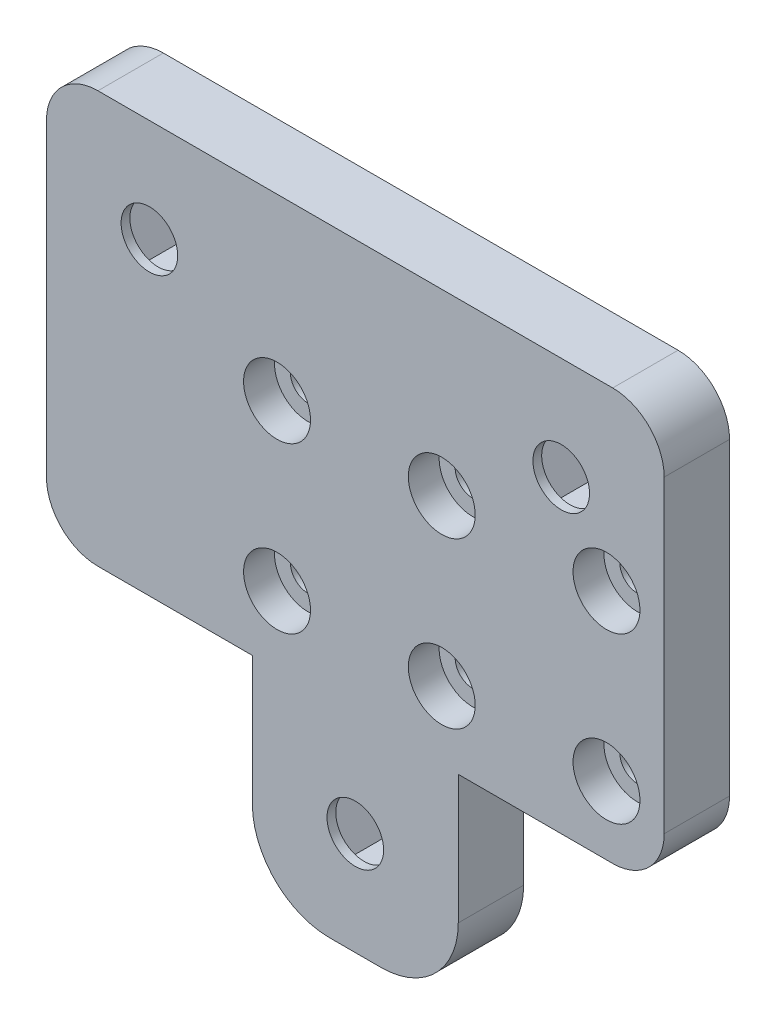
SolidWorks part; units mm, degrees
ref_plane "Front Plane" through (0, 0, 0) normal (0, 0, 1) x (1, 0, 0)
ref_plane "Top Plane" through (0, 0, 0) normal (0, 1, 0) x (1, 0, 0)
ref_plane "Right Plane" through (0, 0, 0) normal (1, 0, 0) x (0, 0, -1)
sketch "Sketch1" plane through (0, 0, 0) normal (0, 0, 1) x (1, 0, 0)
  line L0 (30, 40) -> (30, -20) construction
  line L1 (5, 0) -> (20, 0)
  line L2 (0, 5) -> (0, 35)
  line L3 (5, 40) -> (55, 40)
  line L4 (60, 5) -> (60, 35)
  line L6 (20, 0) -> (20, -12.5)
  line L7 (27.5, -20) -> (32.5, -20)
  line L8 (40, 0) -> (40, -12.5)
  line L9 (40, 0) -> (55, 0)
  arc A0 (5, 0) -> (0, 5) centre (5, 5) cw
  arc A1 (55, 0) -> (60, 5) centre (55, 5) ccw
  arc A2 (55, 40) -> (60, 35) centre (55, 35) cw
  arc A3 (0, 35) -> (5, 40) centre (5, 35) cw
  arc A4 (20, -12.5) -> (27.5, -20) centre (27.5, -12.5) ccw
  arc A5 (32.5, -20) -> (40, -12.5) centre (32.5, -12.5) ccw
  point P7 (0, 0)
  point P10 (60, 0)
  point P15 (0, 40)
  point P24 (20, -20)
  point P27 (40, -20)
  point P32 (20, 0)
  dimension "D3" = 5
  dimension "D6" = 7.5
  dimension "D1" = 60
  dimension "D2" = 40
  dimension "D4" = 20
  dimension "D5" = 20
extrude "Boss-Extrude1" add sketch "Sketch1" along normal blind 6.35
hole_wizard "M5 Clearance Hole1" positions "Sketch3" profile "Sketch4" hole size "M5" standard "ANSI Metric" end condition through all
sketch "Sketch3" plane through (0, 0, 6.35) normal (0, 0, 1) x (1, 0, 0)
  line L0 (30, 40) -> (30, -20) construction
  line L1 (55, 40) -> (5, 40) construction
  line L3 (27.5, -20) -> (32.5, -20) construction
  point P12 (10, 30)
  point P15 (50, 30)
  point P19 (30, -10)
  dimension "D1" = 20
  dimension "D2" = 10
  dimension "D3" = 10
sketch "Sketch4" plane through (30, -10, 6.35) normal (1, 0, 0) x (0, -1, 0)
  line L0 (0, 0) -> (0, 6.35)
  line L1 (0, 6.35) -> (2.75, 6.35)
  line L2 (2.75, 6.35) -> (2.75, 0)
  line L5 (2.75, 0) -> (0, 0)
  line L11 (0, -6.35) -> (0, 107.95) construction
  dimension "Thru Hole Dia." = 5.5
  dimension "Thru Hole Depth" = 6.35
hole_wizard "CBORE for M3 SHCS1" positions "Sketch5" profile "Sketch6" counterbore size "M3" standard "ANSI Metric" end condition through all
sketch "Sketch5" plane through (0, 0, 6.35) normal (0, 0, 1) x (1, 0, 0)
  line L2 (38.3967, 22.6258) -> (38.3967, 6.6258)
  line L3 (38.3967, 6.6258) -> (54.3967, 6.6258)
  line L4 (54.3967, 22.6258) -> (54.3967, 6.6258)
  line L6 (38.3967, 22.6258) -> (54.3967, 22.6258)
  line L13 (38.3967, 22.6258) -> (22.3967, 22.6258)
  line L16 (22.3967, 22.6258) -> (38.3967, 22.6258)
  line L17 (22.3967, 22.6258) -> (22.3967, 6.6258)
  line L18 (22.3967, 6.6258) -> (38.3967, 6.6258)
  line L19 (38.3967, 22.6258) -> (38.3967, 6.6258)
  point P0 (38.3967, 22.6258)
  point P4 (54.3967, 6.6258)
  point P89 (38.3967, 6.6258)
  point P90 (54.3967, 22.6258)
  point P384 (22.3967, 6.6258)
  point P387 (22.3967, 22.6258)
  dimension "D1" = 16
  dimension "D2" = 16
  dimension "D3" = 16
sketch "Sketch6" plane through (38.3967, 22.6258, 6.35) normal (1, 0, 0) x (0, -1, 0)
  line L0 (0, 0) -> (0, 6.35)
  line L1 (0, 6.35) -> (1.7, 6.35)
  line L3 (1.7, 6.35) -> (1.7, 3)
  line L4 (1.7, 3) -> (3.25, 3)
  line L5 (3.25, 3) -> (3.25, 0)
  line L7 (3.25, 0) -> (0, 0)
  line L11 (0, -6.35) -> (0, 107.95) construction
  dimension "Thru Hole Dia." = 3.4
  dimension "Thru Hole Depth" = 6.35
  dimension "C'Bore Dia." = 6.5
  dimension "C'Bore Depth" = 3
sketch "Sketch7" plane through (0, 0, 0) normal (0, 0, -1) x (-1, 0, 0)
  line L1 (-45.2657, 30) -> (-47.6329, 34.1)
  line L2 (-47.6329, 34.1) -> (-52.3671, 34.1)
  line L3 (-52.3671, 34.1) -> (-54.7343, 30)
  line L4 (-54.7343, 30) -> (-52.3671, 25.9)
  line L5 (-52.3671, 25.9) -> (-47.6329, 25.9)
  line L6 (-47.6329, 25.9) -> (-45.2657, 30)
  line L7 (-5.2657, 30) -> (-7.6329, 34.1)
  line L8 (-7.6329, 34.1) -> (-12.3671, 34.1)
  line L9 (-12.3671, 34.1) -> (-14.7343, 30)
  line L10 (-14.7343, 30) -> (-12.3671, 25.9)
  line L11 (-12.3671, 25.9) -> (-7.6329, 25.9)
  line L12 (-7.6329, 25.9) -> (-5.2657, 30)
  line L13 (-25.2657, -10) -> (-27.6329, -5.9)
  line L14 (-27.6329, -5.9) -> (-32.3671, -5.9)
  line L15 (-32.3671, -5.9) -> (-34.7343, -10)
  line L16 (-34.7343, -10) -> (-32.3671, -14.1)
  line L17 (-32.3671, -14.1) -> (-27.6329, -14.1)
  line L18 (-27.6329, -14.1) -> (-25.2657, -10)
  circle A0 centre (-50, 30) radius 4.1 construction
  circle A1 centre (-10, 30) radius 4.1 construction
  circle A2 centre (-30, -10) radius 4.1 construction
  dimension "D1" = 8.2
  dimension "D2" = 8.2
  dimension "D3" = 8.2
extrude "Cut-Extrude1" cut sketch "Sketch7" against normal blind 5.5
hole_wizard "M5x0.8 Tapped Hole1" [suppressed] positions "3DSketch1" profile "Sketch8" tap size "M5x0.8" standard "ANSI Metric"
sketch3d "3DSketch1"
  point P0 (10, 30, 7.5)
  point P3 (50, 30, 7.5)
  point P6 (30, -10, 7.5)
sketch "Sketch8" plane through (10, 30, 7.5) normal (1, 0, 0) x (0, -1, 0)
  line L0 (0, 0) -> (0, 7.5)
  line L1 (0, 7.5) -> (2.1, 7.5)
  line L2 (2.1, 7.5) -> (2.1, 0)
  line L5 (2.1, 0) -> (0, 0)
  line L11 (0, -6.35) -> (0, 107.95) construction
  dimension "Thru Tap Drill Dia." = 4.2
  dimension "Thru Tap Drill Depth" = 7.5
cosmetic thread "Hole Thread1" [suppressed] parameters "D2"=5
cosmetic thread "Hole Thread2" [suppressed] parameters "D2"=5
cosmetic thread "Hole Thread3" [suppressed] parameters "D2"=5
